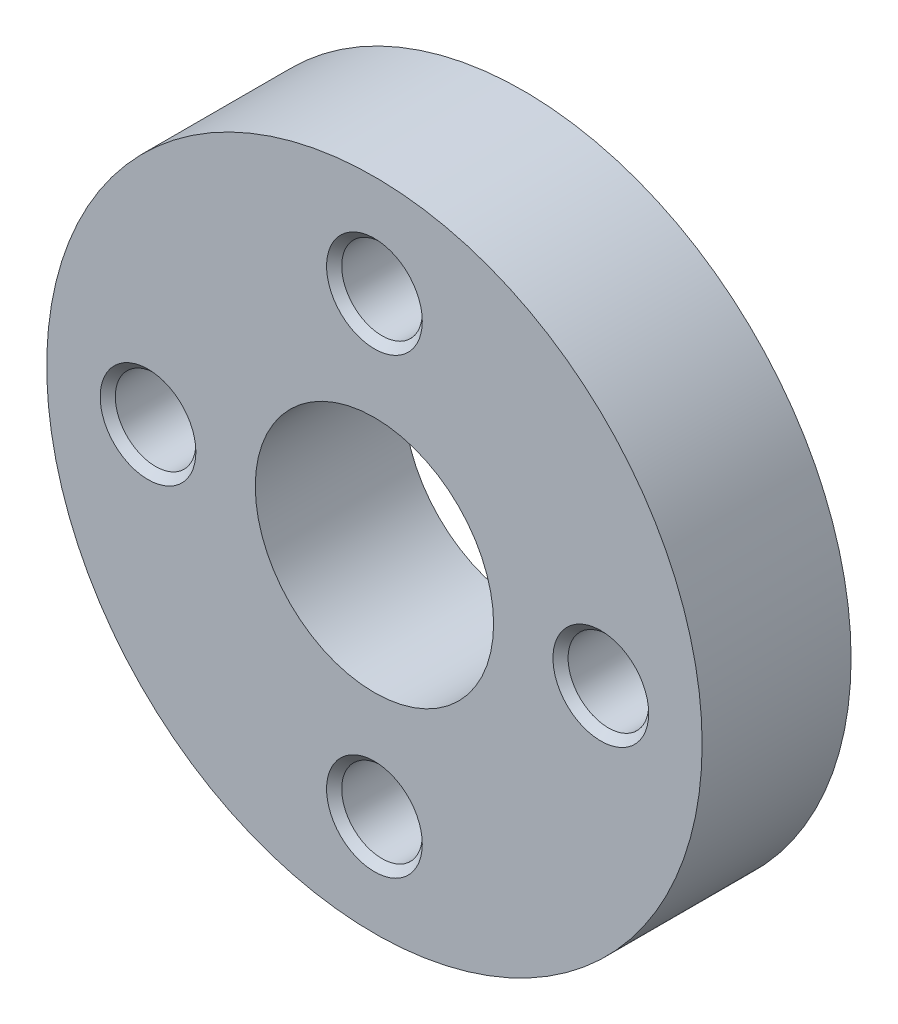
SolidWorks part; units mm, degrees
material "6061-T6 (SS)"
ref_plane "Front Plane" through (0, 0, 0) normal (0, 0, 1) x (1, 0, 0)
ref_plane "Top Plane" through (0, 0, 0) normal (0, 1, 0) x (1, 0, 0)
ref_plane "Right Plane" through (0, 0, 0) normal (1, 0, 0) x (0, 0, -1)
sketch "Sketch1" plane through (0, 0, 0) normal (0, 0, 1) x (1, 0, 0)
  circle A0 centre (0, 0) radius 11
  dimension "D1" = 22
extrude "Extrude1" add sketch "Sketch1" against normal mid plane 5
sketch "Sketch2" plane through (0, 0, 2.5) normal (0, 0, 1) x (1, 0, 0)
  circle A0 centre (0, 0) radius 4
  dimension "D1" = 8
hole_wizard "#6-32 Tapped Hole3" positions "3DSketch4" profile "Sketch7" tap size "#6-32" standard "Ansi Inch" end condition through all
sketch3d "3DSketch4"
  line L0 (0, 0, 0) -> (13.2813, 0, 0) construction
  line L1 (13.2813, 0, 0) -> (-13.4508, 0, 0) construction
  line L3 (0, 0, 0) -> (0, -11.5868, 0) construction
  line L4 (0, -11.5868, 0) -> (0, 11.7986, 0) construction
  point P0 (0, 7.5993, 2.5)
  point P2 (-7.5993, 0, 2.5)
  point P4 (7.5993, 0, 2.5)
  point P6 (0, -7.5993, 2.5)
  dimension "D1" = 8
  dimension "D2" = 8
  dimension "D3" = 8
  dimension "D4" = 8
sketch "Sketch7" plane through (0, 7.5993, 2.5) normal (1, 0, 0) x (0, -1, 0)
  line L0 (0, 0) -> (0, 5)
  line L1 (0, 5) -> (1.3525, 5)
  line L2 (1.3525, 5) -> (1.3525, 0)
  line L5 (1.3525, 0) -> (0, 0)
  line L11 (0, -6.35) -> (0, 107.95) construction
  dimension "Thru Tap Drill Dia." = 2.7051
  dimension "Thru Tap Drill Depth" = 5
cosmetic thread "Hole Thread4" parameters "D2"=3.5052
cosmetic thread "Hole Thread5" parameters "D2"=3.5052
cosmetic thread "Hole Thread6" parameters "D2"=3.5052
cosmetic thread "Hole Thread7" parameters "D2"=3.5052
hole_wizard "#10-32 Tapped Hole2" [suppressed] positions "3DSketch7" profile "Sketch12" tap size "#10-32" standard "Ansi Inch"
sketch3d "3DSketch7"
  point P0 (-7.7838, 7.7725, -3.3516)
sketch "Sketch12" plane through (-7.7838, 7.7725, -3.3516) normal (0, 0, 1) x (-0.7066, -0.7076, 0)
  line L0 (0, 0) -> (0, 12.7957)
  line L1 (0, 12.7957) -> (2.0193, 11.5824)
  line L2 (2.0193, 11.5824) -> (2.0193, 0)
  line L5 (2.0193, 0) -> (0, 0)
  line L10 (0, 12.7957) -> (-2.0193, 11.5824) construction
  line L11 (0, -6.35) -> (0, 107.95) construction
  dimension "Tap Drill Dia." = 4.0386
  dimension "Tap Drill Depth" = 11.5824
  dimension "Drill Angle" = 118
cosmetic thread "Hole Thread9" [suppressed] parameters "D1"=9.6126, "D2"=4.826
chamfer "Chamfer1" distance 0.254 angle 45 8 edges at (1.3525, 7.5993, 2.5) (1.3525, -7.5993, -2.5) (-6.2468, 0, -2.5) (1.3525, 7.5993, -2.5) (8.9519, 0, -2.5) (8.9519, 0, 2.5) (1.3525, -7.5993, 2.5) (-6.2468, 0, 2.5)
chamfer "Chamfer4" [suppressed] distance 0.254 angle 45
extrude "Extrude2" cut sketch "Sketch2" against normal through all
